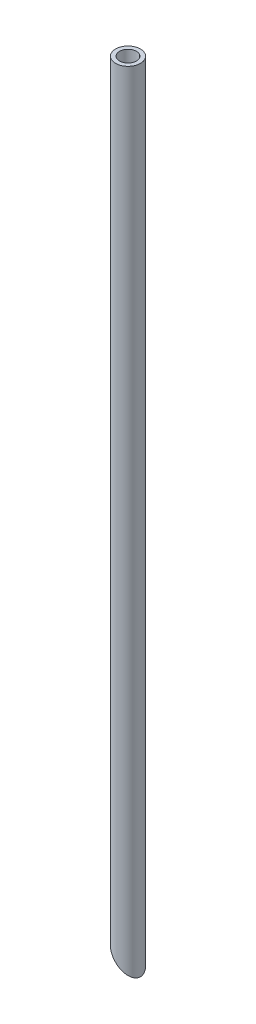
SolidWorks part; units mm, degrees
ref_plane "Front Plane" through (0, 0, 0) normal (0, 0, 1) x (1, 0, 0)
ref_plane "Top Plane" through (0, 0, 0) normal (0, 1, 0) x (1, 0, 0)
ref_plane "Right Plane" through (0, 0, 0) normal (1, 0, 0) x (0, 0, -1)
sketch "Sketch1" plane through (0, 0, 0) normal (0, 1, 0) x (1, 0, 0)
  circle A0 centre (0, 0) radius 0.16
  circle A1 centre (0, 0) radius 0.2362
  dimension "D1" = 0.4724
  dimension "D2" = 0.32
extrude "Inner Polyimide" add sketch "Sketch1" along normal blind 15
sketch "Sketch2" plane through (0, 0, 0) normal (0, 0, 1) x (1, 0, 0)
  line L0 (0.2362, 0) -> (-0.2362, 0.4724)
  line L1 (-0.2362, 15) -> (-0.2362, 0) construction
  line L2 (-0.2362, 0.4724) -> (-0.2362, 0)
  line L3 (-0.2362, 0) -> (0.2362, 0)
  dimension "D1" = 45
extrude "Cut-Extrude1" cut sketch "Sketch2" against normal through all and the other way through all
